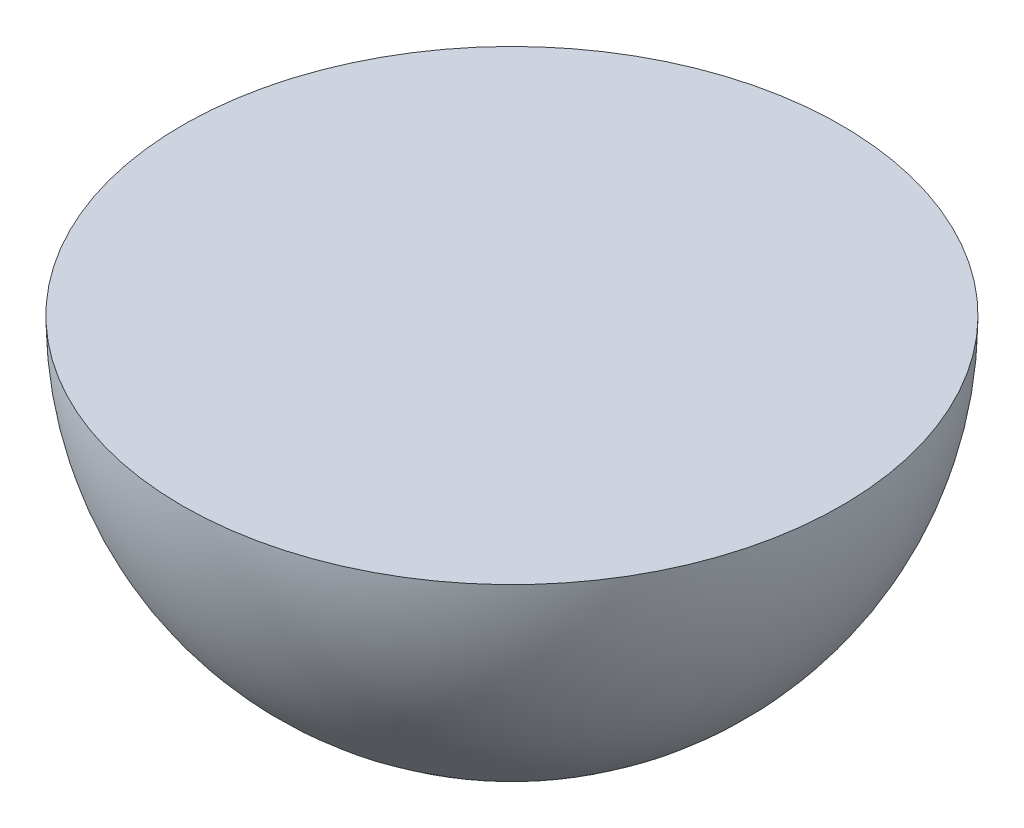
SolidWorks part; units mm, degrees
material "Pure Gold"
ref_plane "Front Plane" through (0, 0, 0) normal (0, 0, 1) x (1, 0, 0)
ref_plane "Top Plane" through (0, 0, 0) normal (0, 1, 0) x (1, 0, 0)
ref_plane "Right Plane" through (0, 0, 0) normal (1, 0, 0) x (0, 0, -1)
sketch "Sketch2" plane through (0, 0, 0) normal (0, 1, 0) x (1, 0, 0)
  line L0 (0, 71.755) -> (0, -71.755)
  arc A0 (0, 71.755) -> (0, -71.755) centre (0, 0) ccw
  dimension "D1" = 143.51
revolve "Revolve1" add sketch "Sketch2" angle 180 about L0
